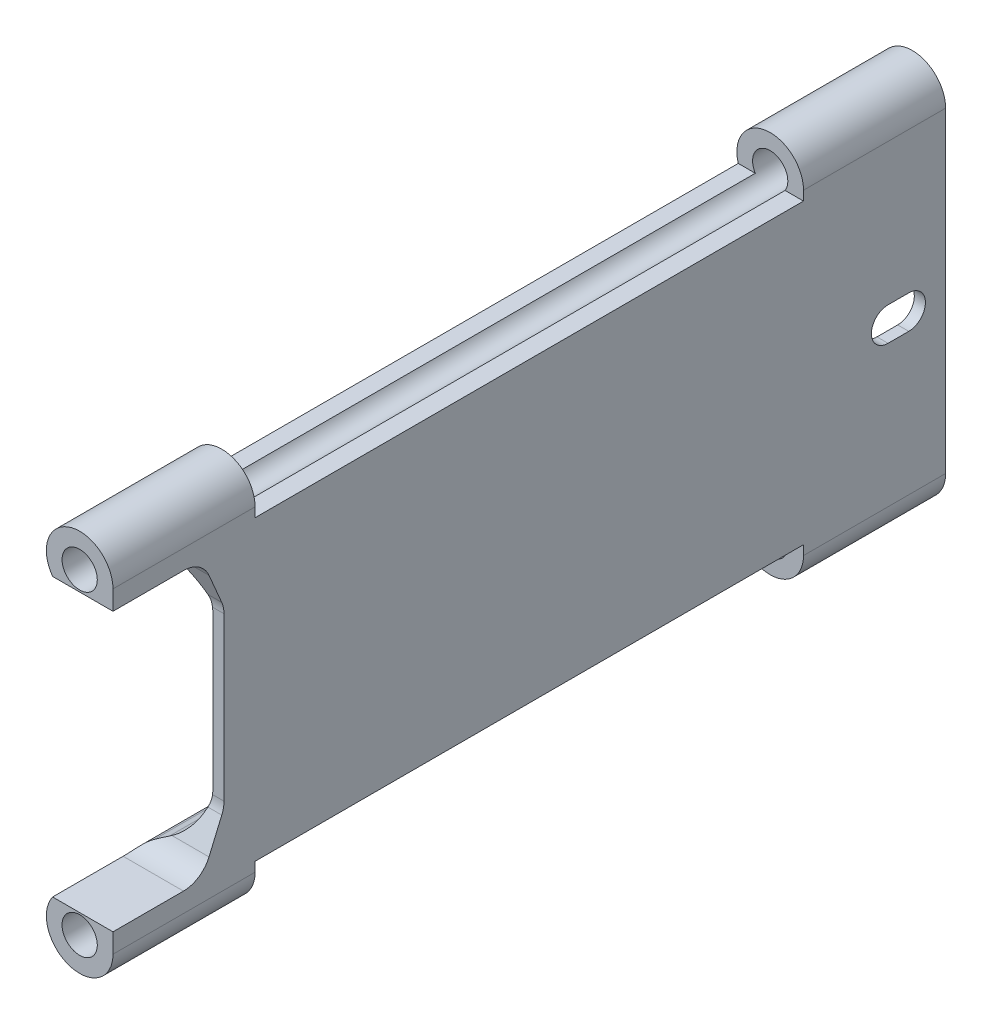
SolidWorks part; units mm, degrees
material "ABS"
ref_plane "Alzado" through (0, 0, 0) normal (0, 0, 1) x (1, 0, 0)
ref_plane "Planta" through (0, 0, 0) normal (0, 1, 0) x (1, 0, 0)
ref_plane "Vista lateral" through (0, 0, 0) normal (1, 0, 0) x (0, 0, -1)
sketch "Croquis1" plane through (0, 0, 0) normal (0, 0, 1) x (1, 0, 0)
  line L5 (-13.465, 0) -> (13.8234, 0) construction
  line L8 (-2, 19.2858) -> (-8.9869, 23.2963)
  line L9 (-2, 19.2858) -> (-2, -19.2858)
  line L10 (0, 28.5) -> (0, -28.5)
  line L11 (-2, -19.2858) -> (-8.9869, -23.2963)
  circle A0 centre (-6, 28.5) radius 3.175
  arc A5 (0, 28.5) -> (-8.9869, 23.2963) centre (-6, 28.5) ccw
  arc A6 (0, -28.5) -> (-8.9869, -23.2963) centre (-6, -28.5) cw
  circle A7 centre (-6, -28.5) radius 3.175
  point P7 (0, 0)
  point P15 (0, 0)
  point P16 (-2, 0)
  point P17 (-2, 0)
  dimension "D1" = 6.35
  dimension "D2" = 57
  dimension "D3" = 2
  dimension "D4" = 6
extrude "Saliente-Extruir1" add sketch "Croquis1" against normal blind 150
fillet "Redondeo1" radius 10 2 edges at (-2, -19.2858, -75) (-2, 19.2858, -75)
sketch "Croquis2" plane through (0, 0, 0) normal (1, 0, 0) x (0, 0, -1)
  line L0 (16, 25) -> (20, 15.6468)
  line L1 (20, 15.6468) -> (20, -15.6468)
  line L2 (-29.8735, 0) -> (35.3957, 0) construction
  line L3 (16, 25) -> (-29.8735, 25)
  line L4 (-29.8735, 25) -> (-29.8735, -25)
  line L5 (16, -25) -> (-29.8735, -25)
  line L6 (16, -25) -> (20, -15.6468)
  line L8 (0, -28.5) -> (0, 28.5) construction
  point P10 (20, 0)
  dimension "D1" = 50
  dimension "D2" = 16
  dimension "D3" = 20
extrude "Cortar-Extruir1" cut sketch "Croquis2" against normal through all
fillet "Redondeo2" radius 5 4 edges at (-1.1171, 15.6468, -20) (-1.1171, -15.6468, -20) (-5.4367, -25, -16) (-5.4367, 25, -16)
sketch "Croquis3" plane through (0, 0, 0) normal (1, 0, 0) x (0, 0, -1)
  line L0 (0, 0) -> (150, 0) construction
  line L1 (25.6041, 44.9478) -> (124.3959, 44.9478)
  line L2 (25.6041, 44.9478) -> (25.6041, 26.8024)
  line L3 (25.6041, 26.8024) -> (124.3959, 26.8024)
  line L4 (124.3959, 44.9478) -> (124.3959, 26.8024)
  line L5 (124.3959, -44.9478) -> (124.3959, -26.8024)
  line L6 (25.6041, -26.8024) -> (124.3959, -26.8024)
  line L7 (25.6041, -44.9478) -> (25.6041, -26.8024)
  line L8 (25.6041, -44.9478) -> (124.3959, -44.9478)
  line L9 (150, 13.4955) -> (150, -13.4955) construction
  point P16 (75, 0)
  point P17 (75, -26.8024)
extrude "Cortar-Extruir2" cut sketch "Croquis3" against normal through all
sketch "Croquis4" plane through (-2, 0, 0) normal (-1, 0, 0) x (0, 0, 1)
  line L0 (-143.3598, 0) -> (-139.6272, 0) construction
  line L1 (-143.3598, 3) -> (-139.6272, 3)
  line L2 (-143.3598, -3) -> (-139.6272, -3)
  arc A0 (-143.3598, 3) -> (-143.3598, -3) centre (-143.3598, 0) ccw
  arc A1 (-139.6272, -3) -> (-139.6272, 3) centre (-139.6272, 0) ccw
  point P2 (-141.4935, 0)
  dimension "D1" = 3
extrude "Cortar-Extruir3" cut sketch "Croquis4" against normal through all
